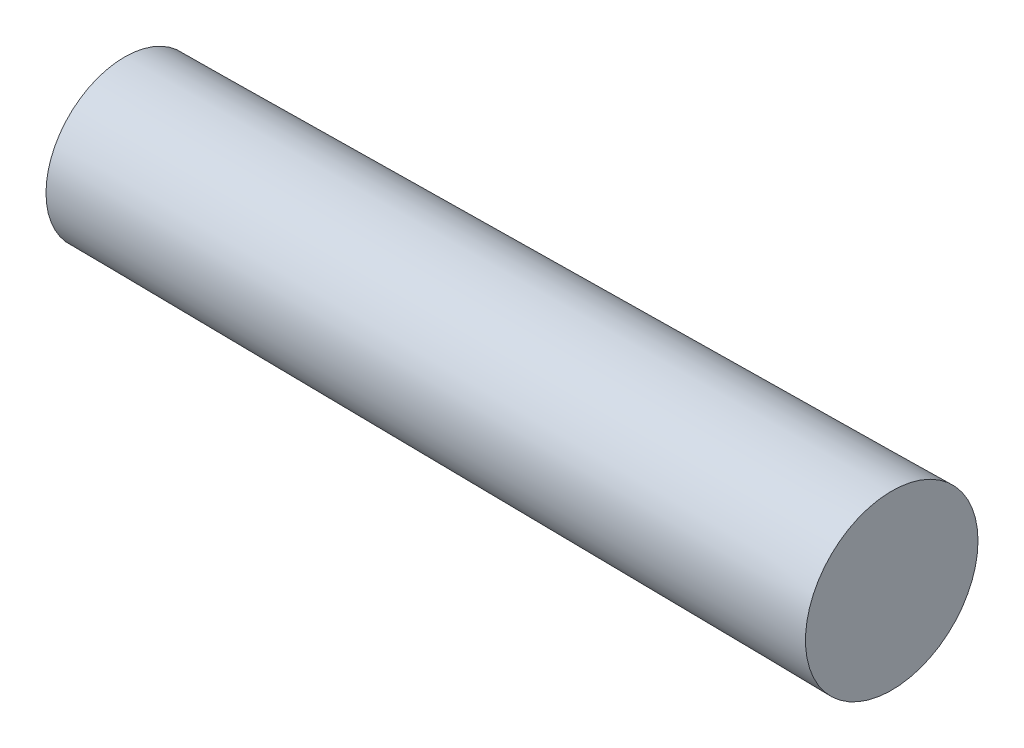
SolidWorks part; units mm, degrees
ref_plane "Plane1" through (0, 0, 0) normal (0, 0, 1) x (1, 0, 0)
ref_plane "Plane2" through (0, 0, 0) normal (0, 1, 0) x (1, 0, 0)
ref_plane "Plane3" through (0, 0, 0) normal (1, 0, 0) x (0, 0, -1)
sketch "Sketch1" plane through (0, 0, 0) normal (0, 0, 1) x (1, 0, 0)
  line L0 (0, 0) -> (210, 0) construction
  line L2 (0.12, 0.5) -> (5.88, 0.5576)
  line L4 (0, 0) -> (6, 0)
  line L5 (0.12, -0.5) -> (5.88, -0.5576) construction
  arc A0 (0.12, 0.5) -> (0, 0) centre (1.1017, 0) ccw
  arc A1 (5.88, 0.5576) -> (6, 0) centre (4.6445, 0) cw
  dimension "Diameter" = 1
  dimension "Length" = 6
  dimension "Crown_ht" = 0.12
  dimension "D1" = 0.12
  dimension "D2" = 0.573
revolve "Base-Revolve" add sketch "Sketch1" angle 360 about L0
ref_plane "Plane4" through (5, 0, 0) normal (1, 0, 0) x (0, 0, -1)
other "SurfaceCut1"
equation "\"D1@Sketch1\" = \"Crown_ht@Sketch1\""
